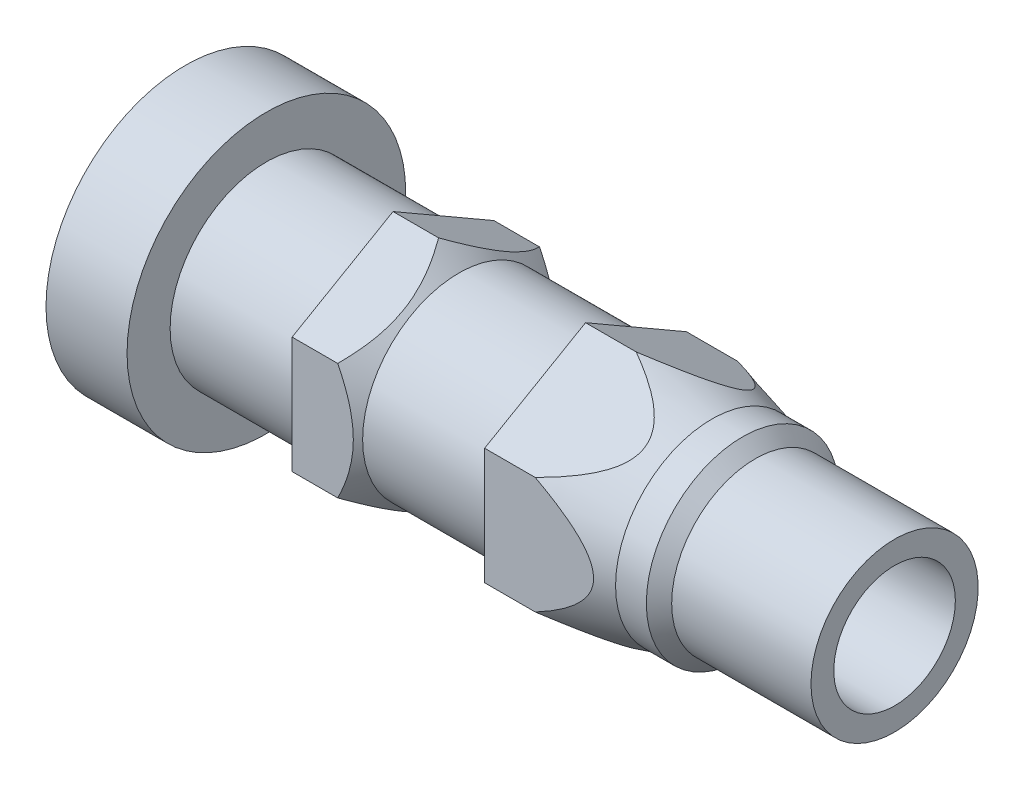
SolidWorks part; units mm, degrees
material "Brass Alloy 385"
ref_plane "Front Plane" through (0, 0, 0) normal (0, 0, 1) x (1, 0, 0)
ref_plane "Top Plane" through (0, 0, 0) normal (0, 1, 0) x (1, 0, 0)
ref_plane "Right Plane" through (0, 0, 0) normal (1, 0, 0) x (0, 0, -1)
sketch "Sketch1" plane through (0, 0, 0) normal (0, 0, 1) x (1, 0, 0)
  line L0 (0.4064, 0.4826) -> (1.0414, 0.4826)
  line L1 (0.4064, 0.6985) -> (0.4064, 0.4826)
  line L2 (0, 0.6985) -> (0.4064, 0.6985)
  line L3 (0, 0) -> (0, 0.6985)
  line L4 (0, 0) -> (3.556, 0)
  line L5 (3.556, 0.4191) -> (3.556, 0)
  line L6 (2.8575, 0.4191) -> (3.556, 0.4191)
  line L7 (2.794, 0.4826) -> (2.8575, 0.4191)
  line L8 (2.6398, 0.4826) -> (2.794, 0.4826)
  line L9 (2.2606, 0.5842) -> (2.6398, 0.4826)
  line L10 (2.0066, 0.5842) -> (2.2606, 0.5842)
  line L11 (2.0066, 0.4826) -> (2.0066, 0.5842)
  line L12 (1.3716, 0.4826) -> (2.0066, 0.4826)
  line L13 (1.27, 0.5842) -> (1.3716, 0.4826)
  line L14 (1.0414, 0.5842) -> (1.27, 0.5842)
  line L15 (1.0414, 0.4826) -> (1.0414, 0.5842)
  line L16 (0, 0) -> (3.556, 0) construction
revolve "RevolutionAngle1" add sketch "Sketch1" angle 360 about L16
hole_wizard "Hole1" positions "Sketch3" profile "Sketch2" legacy
sketch "Sketch3" plane through (0, 0, 0) normal (-1, 0, 0) x (0, 0, 1)
  point P0 (0, 0)
sketch "Sketch2" plane through (0, 0, 0) normal (0, 1, 0) x (0, 0, 1)
  line L0 (0, 0) -> (0, 2.5226)
  line L1 (0, 2.5226) -> (0.3937, 2.286)
  line L2 (0.3937, 2.286) -> (0.3937, 0.198)
  line L3 (0.3937, 0.198) -> (0.508, 0)
  line L4 (0.508, 0) -> (0, 0)
  line L5 (0, -14.3089) -> (0, 102.4216) construction
  line L6 (0, 2.5226) -> (-0.3937, 2.286) construction
  line L7 (-0.3937, 0.198) -> (-0.508, 0) construction
  dimension "A1" = 0.7874
  dimension "N" = 2.286
  dimension "B" = 1.016
  dimension "P1" = 60
  dimension "Drill Angle" = 118
hole_wizard "Hole2" positions "3DSketch1" profile "Sketch7" legacy end condition through all
sketch3d "3DSketch1"
  line L0 (3.556, 0, 0) -> (2.8575, 0, 0) construction
  point P0 (3.556, 0, 0)
sketch "Sketch7" plane through (3.556, 0, 0) normal (0, 1, 0) x (0, 0, -1)
  line L0 (0, 0) -> (0, 3.556)
  line L1 (0, 3.556) -> (0.3048, 3.556)
  line L2 (0.3048, 3.556) -> (0.3048, 0)
  line L3 (0.3048, 0) -> (0, 0)
  line L4 (0, 110) -> (0, -10) construction
  dimension "A2" = 0.6096
  dimension "Depth" = 3.556
sketch "Sketch6" plane through (1.0414, 0, 0) normal (-1, 0, 0) x (0, 0, 1)
  line L1 (0, 0.5842) -> (-0.5059, 0.2921)
  line L2 (-0.5059, 0.2921) -> (-0.5059, -0.2921)
  line L3 (-0.5059, -0.2921) -> (0, -0.5842)
  line L4 (0, -0.5842) -> (0.5059, -0.2921)
  line L5 (0.5059, -0.2921) -> (0.5059, 0.2921)
  line L6 (0.5059, 0.2921) -> (0, 0.5842)
  circle A0 centre (0, 0) radius 0.5059 construction
  circle A1 centre (0, 0) radius 0.635
  dimension "D3" = 1.27
  dimension "E" = 1.1684
  dimension "D2" = 0.2921
extrude "ExtrusionBlind1" cut sketch "Sketch6" along a picked direction on the side against the normal blind 1.6764
